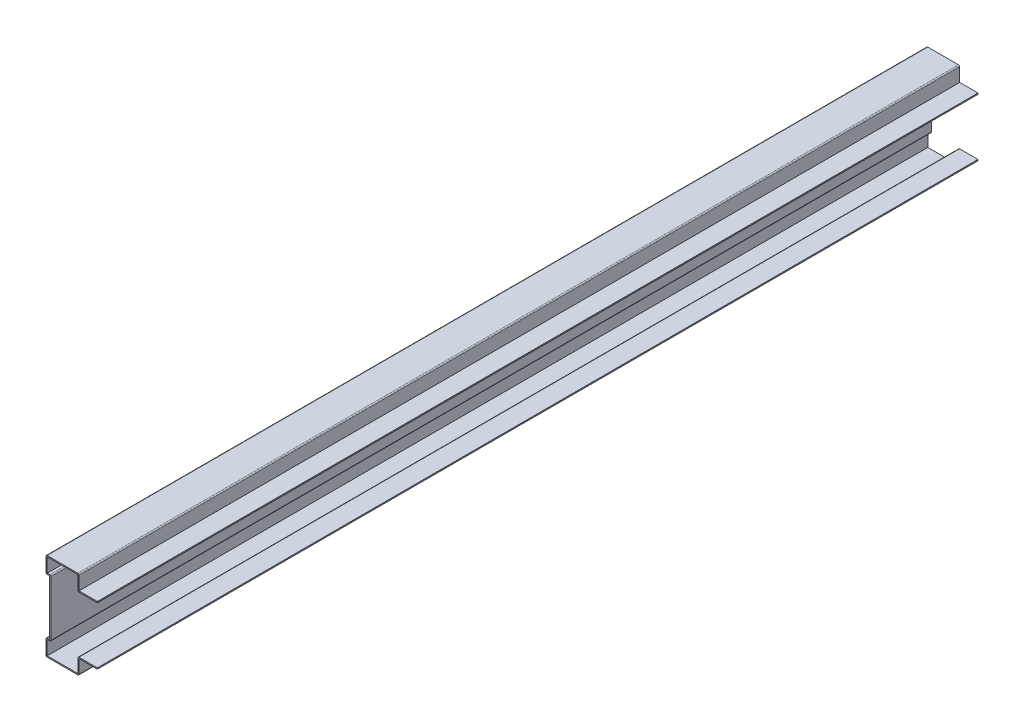
SolidWorks part; units mm, degrees
ref_plane "Front Plane" through (0, 0, 0) normal (0, 0, 1) x (1, 0, 0)
ref_plane "Top Plane" through (0, 0, 0) normal (0, 1, 0) x (1, 0, 0)
ref_plane "Right Plane" through (0, 0, 0) normal (1, 0, 0) x (0, 0, -1)
sketch "Sketch1" plane through (0, 0, 0) normal (0, 0, 1) x (1, 0, 0)
  line L0 (0, 0) -> (-15.875, 0)
  line L1 (-15.875, 0) -> (-15.875, -12.7)
  line L2 (-15.875, -12.7) -> (-44.45, -12.7)
  line L3 (-44.45, -12.7) -> (-44.45, 1.5875)
  line L4 (-44.45, 1.5875) -> (-41.275, 1.5875)
  line L5 (-41.275, 1.5875) -> (-41.275, 49.2125)
  line L6 (-41.275, 49.2125) -> (-44.45, 49.2125)
  line L7 (-44.45, 49.2125) -> (-44.45, 63.5)
  line L8 (-44.45, 63.5) -> (-15.875, 63.5)
  line L9 (-15.875, 63.5) -> (-15.875, 50.8)
  line L10 (-15.875, 50.8) -> (0, 50.8)
  point P8 (0, 0)
  point P14 (-51.8214, -22.3731)
  point P15 (-54.7168, 50.8)
  dimension "D1" = 50.8
  dimension "D2" = 76.2
  dimension "D3" = 12.7
  dimension "D4" = 14.2875
  dimension "D5" = 3.175
  dimension "D6" = 47.625
  dimension "D7" = 28.575
  dimension "D8" = 12.7
  dimension "D9" = 44.45
extrude "Extrude-Thin1" add sketch "Sketch1" against normal blind 762 thin
fillet "Fillet1" radius 1.016 10 edges at (-16.891, 1.016, -381) (-15.875, -12.7, -381) (-44.45, -12.7, -381) (-44.45, 1.5875, -381) (-40.259, 0.5715, -381) (-40.259, 50.2285, -381) (-44.45, 49.2125, -381) (-44.45, 63.5, -381) (-15.875, 63.5, -381) (-16.891, 49.784, -381)
